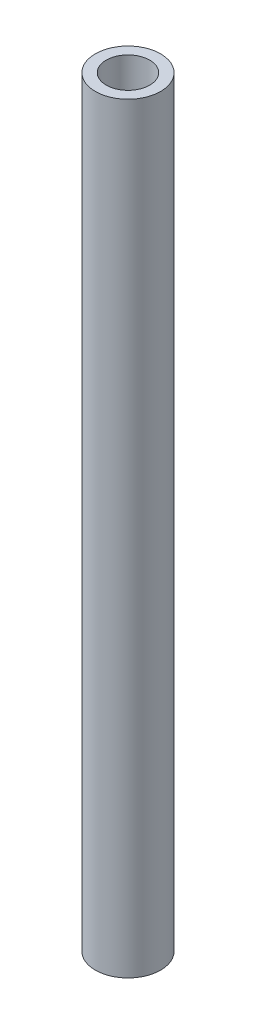
SolidWorks part; units mm, degrees
ref_plane "정면" through (0, 0, 0) normal (0, 0, 1) x (1, 0, 0)
ref_plane "윗면" through (0, 0, 0) normal (0, 1, 0) x (1, 0, 0)
ref_plane "우측면" through (0, 0, 0) normal (1, 0, 0) x (0, 0, -1)
sketch "스케치1" plane through (0, 0, 0) normal (0, 1, 0) x (1, 0, 0)
  circle A0 centre (0, 0) radius 3
  circle A1 centre (0, 0) radius 2
  dimension "D1" = 1
  dimension "D2" = 6
extrude "보스-돌출1" add sketch "스케치1" along normal blind 70
